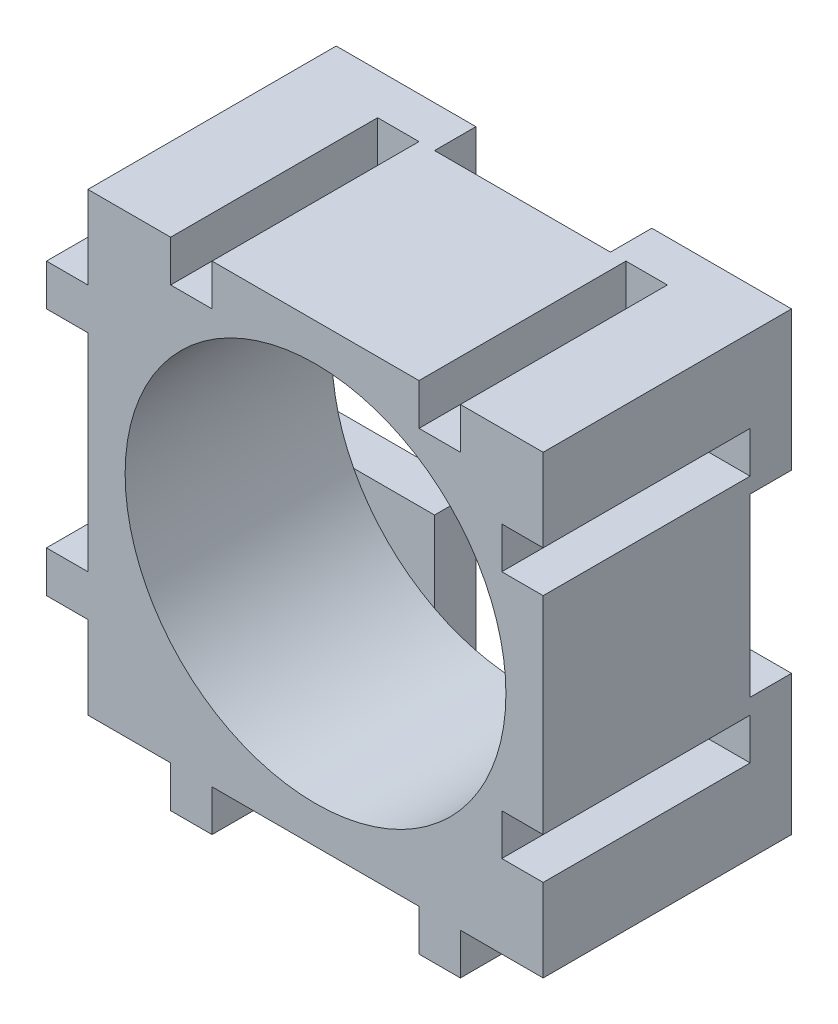
SolidWorks part; units mm, degrees
material "ABS"
ref_plane "Front Plane" through (0, 0, 0) normal (0, 0, 1) x (1, 0, 0)
ref_plane "Top Plane" through (0, 0, 0) normal (0, 1, 0) x (1, 0, 0)
ref_plane "Right Plane" through (0, 0, 0) normal (1, 0, 0) x (0, 0, -1)
sketch "Sketch1" plane through (0, 0, 0) normal (0, 0, 1) x (1, 0, 0)
  line L1 (-9.3991, 9.2441) -> (12.6009, 9.2441)
  line L2 (-9.3991, 9.2441) -> (-9.3991, -12.7559)
  line L3 (-9.3991, -12.7559) -> (12.6009, -12.7559)
  line L4 (12.6009, 9.2441) -> (12.6009, -12.7559)
  dimension "D1" = 22
  dimension "D2" = 22
extrude "Boss-Extrude1" add sketch "Sketch1" along normal blind 10
sketch "Sketch3" plane through (0, -12.7559, 0) normal (0, -1, 0) x (1, 0, 0)
  line L0 (-9.3991, 0) -> (12.6009, 0) construction
  line L1 (8.6009, 0) -> (6.6009, 0)
  line L2 (8.6009, 0) -> (8.6009, 10)
  line L3 (8.6009, 10) -> (6.6009, 10)
  line L4 (6.6009, 0) -> (6.6009, 10)
  line L5 (-9.3991, 10) -> (12.6009, 10) construction
  line L6 (-9.3991, 10) -> (-9.3991, 0) construction
  line L7 (-3.3991, 0) -> (-5.3991, 0)
  line L8 (-3.3991, 0) -> (-3.3991, 10)
  line L9 (-3.3991, 10) -> (-5.3991, 10)
  line L10 (-5.3991, 0) -> (-5.3991, 10)
  dimension "D1" = 2
  dimension "D2" = 2
  dimension "D3" = 10
  dimension "D4" = 4
extrude "Boss-Extrude2" add sketch "Sketch3" along normal blind 2
sketch "Sketch4" plane through (-9.3991, 0, 0) normal (-1, 0, 0) x (0, 0, 1)
  line L0 (0, 9.2441) -> (0, -12.7559) construction
  line L1 (0, 5.2441) -> (10, 5.2441)
  line L2 (0, 5.2441) -> (0, 3.2441)
  line L3 (0, 3.2441) -> (10, 3.2441)
  line L4 (10, 5.2441) -> (10, 3.2441)
  line L5 (10, 9.2441) -> (10, -12.7559) construction
  line L7 (0, -8.7559) -> (10, -8.7559)
  line L8 (0, -8.7559) -> (0, -6.7559)
  line L9 (0, -6.7559) -> (10, -6.7559)
  line L10 (10, -8.7559) -> (10, -6.7559)
  line L11 (10, 9.2441) -> (0, 9.2441) construction
  dimension "D1" = 10
  dimension "D2" = 4
  dimension "D3" = 2
  dimension "D4" = 2
extrude "Boss-Extrude3" add sketch "Sketch4" along normal blind 2
sketch "Sketch5" plane through (12.6009, 0, 0) normal (1, 0, 0) x (0, 0, -1)
  line L0 (0, -12.7559) -> (0, 9.2441) construction
  line L1 (0, 5.2441) -> (-10, 5.2441)
  line L2 (0, 5.2441) -> (0, 3.2441)
  line L3 (0, 3.2441) -> (-10, 3.2441)
  line L4 (-10, 5.2441) -> (-10, 3.2441)
  line L5 (-10, -12.7559) -> (-10, 9.2441) construction
  line L6 (-10, -12.7559) -> (0, -12.7559) construction
  line L7 (0, -6.7559) -> (-10, -6.7559)
  line L8 (0, -6.7559) -> (0, -8.7559)
  line L9 (0, -8.7559) -> (-10, -8.7559)
  line L10 (-10, -6.7559) -> (-10, -8.7559)
  dimension "D1" = 2
  dimension "D2" = 2
  dimension "D3" = 10
  dimension "D4" = 4
extrude "Cut-Extrude1" cut sketch "Sketch5" against normal blind 2
sketch "Sketch6" plane through (0, 9.2441, 0) normal (0, 1, 0) x (1, 0, 0)
  line L0 (12.6009, 0) -> (-9.3991, 0) construction
  line L1 (-5.3991, 0) -> (-3.3991, 0)
  line L2 (-5.3991, 0) -> (-5.3991, -10)
  line L3 (-5.3991, -10) -> (-3.3991, -10)
  line L4 (-3.3991, 0) -> (-3.3991, -10)
  line L5 (12.6009, -10) -> (-9.3991, -10) construction
  line L6 (12.6009, -10) -> (12.6009, 0) construction
  line L7 (6.6009, 0) -> (8.6009, 0)
  line L8 (6.6009, 0) -> (6.6009, -10)
  line L9 (6.6009, -10) -> (8.6009, -10)
  line L10 (8.6009, 0) -> (8.6009, -10)
  dimension "D1" = 2
  dimension "D2" = 2
  dimension "D3" = 10
  dimension "D4" = 4
extrude "Cut-Extrude2" cut sketch "Sketch6" against normal blind 2
sketch "Sketch7" plane through (0, 0, 10) normal (0, 0, 1) x (1, 0, 0)
  line L0 (12.6009, -6.7559) -> (12.6009, 3.2441) construction
  line L1 (-3.3991, -12.7559) -> (6.6009, -12.7559) construction
  circle A0 centre (1.6009, -1.7559) radius 9.2
  dimension "D1" = 18.4
  dimension "D3" = 11
  dimension "D2" = 11
extrude "Cut-Extrude3" cut sketch "Sketch7" against normal through all
sketch "Sketch8" plane through (0, 0, 0) normal (0, 0, -1) x (-1, 0, 0)
  line L1 (9.3991, 9.2441) -> (2.6491, 9.2441)
  line L2 (9.3991, 9.2441) -> (9.3991, 2.4941)
  line L3 (9.3991, 2.4941) -> (2.6491, 2.4941)
  line L4 (2.6491, 9.2441) -> (2.6491, 2.4941)
  line L5 (-12.6009, 9.2441) -> (-5.8509, 9.2441)
  line L6 (-12.6009, 9.2441) -> (-12.6009, 2.4941)
  line L7 (-12.6009, 2.4941) -> (-5.8509, 2.4941)
  line L8 (-5.8509, 9.2441) -> (-5.8509, 2.4941)
  line L9 (-12.6009, -12.7559) -> (-5.8509, -12.7559)
  line L10 (-12.6009, -12.7559) -> (-12.6009, -6.0059)
  line L11 (-12.6009, -6.0059) -> (-5.8509, -6.0059)
  line L12 (-5.8509, -12.7559) -> (-5.8509, -6.0059)
  line L13 (9.3991, -12.7559) -> (2.6491, -12.7559)
  line L14 (9.3991, -12.7559) -> (9.3991, -6.0059)
  line L15 (9.3991, -6.0059) -> (2.6491, -6.0059)
  line L16 (2.6491, -12.7559) -> (2.6491, -6.0059)
  dimension "D1" = 8.5
  dimension "D2" = 6.75
  dimension "D3" = 6.75
  dimension "D4" = 6.75
  dimension "D5" = 6.75
  dimension "D6" = 6.75
  dimension "D7" = 8.5
  dimension "D8" = 6.75
extrude "Boss-Extrude4" add sketch "Sketch8" along normal blind 2
